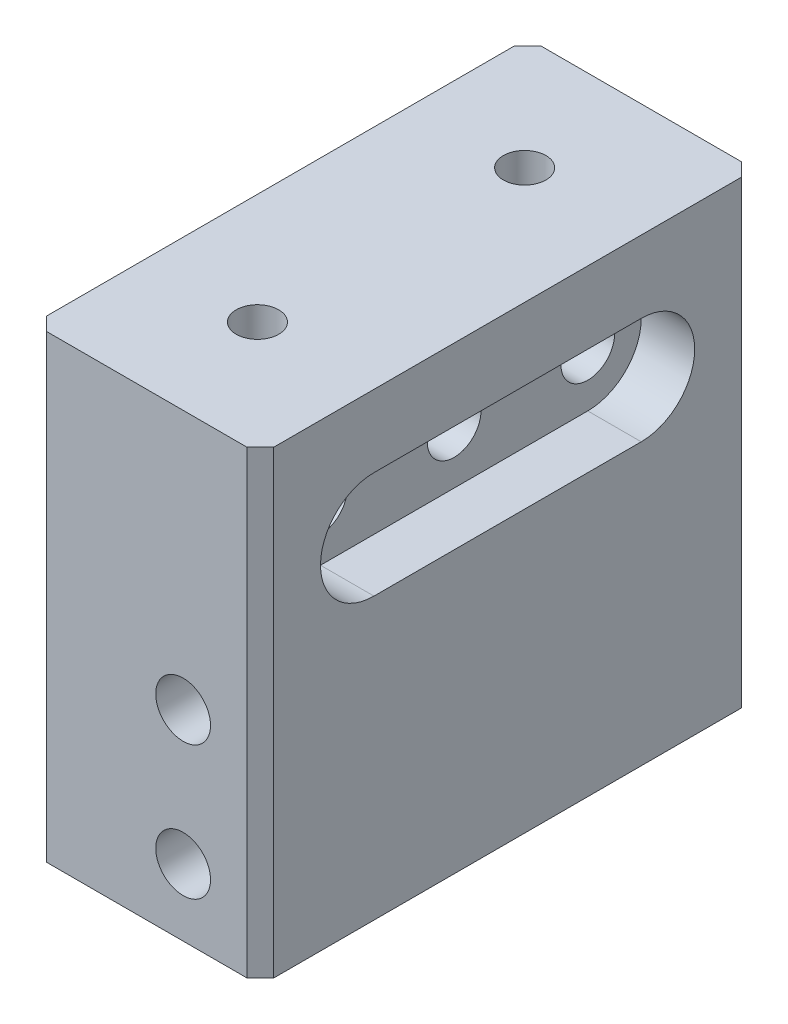
SolidWorks part; units mm, degrees
material "Nylon 101"
ref_plane "Front Plane" through (0, 0, 0) normal (0, 0, 1) x (1, 0, 0)
ref_plane "Top Plane" through (0, 0, 0) normal (0, 1, 0) x (1, 0, 0)
ref_plane "Right Plane" through (0, 0, 0) normal (1, 0, 0) x (0, 0, -1)
sketch "Sketch1" plane through (0, 0, 0) normal (0, 1, 0) x (1, 0, 0)
  line L1 (-10.795, -23.495) -> (10.795, -23.495)
  line L2 (-10.795, -23.495) -> (-10.795, 23.495)
  line L3 (-10.795, 23.495) -> (10.795, 23.495)
  line L4 (10.795, -23.495) -> (10.795, 23.495)
  line L5 (-10.795, -23.495) -> (10.795, 23.495) construction
  line L6 (-10.795, 23.495) -> (10.795, -23.495) construction
  point P0 (0, 0)
  dimension "D1" = 21.59
  dimension "D2" = 46.99
extrude "Boss-Extrude1" add sketch "Sketch1" along normal mid plane 38.1
sketch "Sketch2" plane through (0, 0, 23.495) normal (0, 0, 1) x (1, 0, 0)
  line L5 (-10.795, 19.05) -> (10.795, 19.05) construction
  circle A1 centre (3.4544, -12.7) radius 2.6035
  circle A2 centre (3.4544, 0) radius 2.6035
  dimension "D3" = 19.05
  dimension "D1" = 7.3406
  dimension "D2" = 5.207
  dimension "D4" = 12.7
extrude "Cut-Extrude1" cut sketch "Sketch2" against normal through all
sketch "Sketch4" plane through (10.795, 0, 0) normal (1, 0, 0) x (0, 0, -1)
  line L0 (-23.495, 19.05) -> (23.495, 19.05) construction
  circle A0 centre (-12.7, 12.7) radius 2.5527
  circle A1 centre (12.7, 12.7) radius 2.5527
  circle A2 centre (0, 12.7) radius 2.5527
  dimension "D5" = 5.1054
  dimension "D1" = 6.35
  dimension "D3" = 12.7
  dimension "D4" = 12.7
extrude "Cut-Extrude3" cut sketch "Sketch4" against normal through all
sketch "Sketch7" plane through (10.795, 0, 0) normal (1, 0, 0) x (0, 0, -1)
  line L0 (-12.7, 12.7) -> (12.7, 12.7) construction
  line L1 (-12.7, 17.78) -> (12.7, 17.78)
  line L2 (-12.7, 7.62) -> (12.7, 7.62)
  arc A0 (-12.7, 17.78) -> (-12.7, 7.62) centre (-12.7, 12.7) ccw
  arc A1 (12.7, 7.62) -> (12.7, 17.78) centre (12.7, 12.7) ccw
  point P4 (0, 12.7)
  dimension "D1" = 5.08
extrude "Cut-Extrude5" cut sketch "Sketch7" against normal blind 5.08
sketch "Sketch8" plane through (0, 19.05, 0) normal (0, 1, 0) x (1, 0, 0)
  line L4 (-10.795, -23.495) -> (10.795, -23.495)
  line L5 (10.795, -23.495) -> (10.795, 23.495)
  line L6 (10.795, 23.495) -> (-10.795, 23.495)
  line L7 (-10.795, 23.495) -> (-10.795, -23.495)
  line L8 (-10.795, -23.495) -> (10.795, -23.495)
  line L9 (10.795, -23.495) -> (10.795, 23.495)
  line L10 (10.795, 23.495) -> (-10.795, 23.495)
  line L11 (-10.795, 23.495) -> (-10.795, -23.495)
  dimension "D1" = 0
extrude "Boss-Extrude2" add sketch "Sketch8" along normal blind 5.588
sketch "Sketch9" plane through (0, 24.638, 0) normal (0, 1, 0) x (1, 0, 0)
  line L0 (-10.795, 0) -> (10.795, 0) construction
  line L1 (-10.795, 23.495) -> (-10.795, -23.495) construction
  line L2 (10.795, -23.495) -> (10.795, 23.495) construction
  circle A0 centre (-0.2794, 12.6969) radius 2.0193
  circle A2 centre (-0.2794, -12.6969) radius 2.0193
  dimension "D2" = 4.0386
  dimension "D1" = 12.7
  dimension "D3" = 10.5156
extrude "Cut-Extrude6" cut sketch "Sketch9" against normal blind 5.08
chamfer "Chamfer1" distance 1.27 angle 45 4 edges at (-10.795, 2.794, 23.495) (10.795, 2.794, 23.495) (-10.795, 2.794, -23.495) (10.795, 2.794, -23.495)
